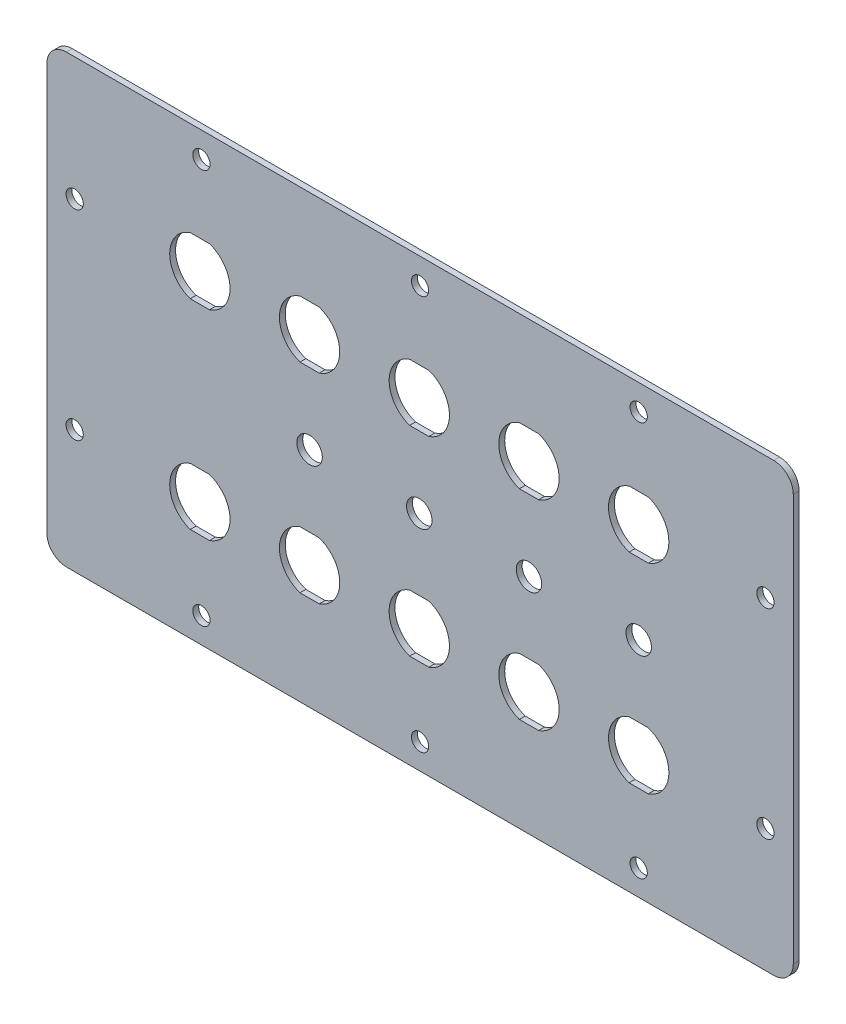
SolidWorks part; units mm, degrees
ref_plane "Front Plane" through (0, 0, 0) normal (0, 0, 1) x (1, 0, 0)
ref_plane "Top Plane" through (0, 0, 0) normal (0, 1, 0) x (1, 0, 0)
ref_plane "Right Plane" through (0, 0, 0) normal (1, 0, 0) x (0, 0, -1)
sketch "Sketch1" plane through (0, 0, 0) normal (0, 0, 1) x (1, 0, 0)
  line L1 (0, 0) -> (190.5, 0)
  line L2 (0, 0) -> (0, 113.82)
  line L3 (0, 113.82) -> (190.5, 113.82)
  line L4 (190.5, 0) -> (190.5, 113.82)
  dimension "D1" = 190.5
  dimension "D2" = 113.82
extrude "Boss-Extrude1" add sketch "Sketch1" along normal blind 1.5
sketch "Sketch2" plane through (0, 0, 0) normal (0, 0, -1) x (-1, 0, 0)
  line L0 (-190.5, 56.91) -> (-183.4, 56.91) construction
  line L1 (-190.5, 0) -> (-190.5, 113.82) construction
  line L2 (-183.4, 56.91) -> (-183.4, 82.41) construction
  line L3 (-183.4, 56.91) -> (-183.4, 31.41) construction
  line L5 (-95.25, 0) -> (-95.25, 113.82) construction
  line L6 (0, 0) -> (-190.5, 0) construction
  line L7 (-190.5, 113.82) -> (0, 113.82) construction
  circle A0 centre (-183.4, 82.41) radius 2.2
  circle A1 centre (-183.4, 31.41) radius 2.2
  circle A2 centre (-7.1, 31.41) radius 2.2
  circle A3 centre (-7.1, 82.41) radius 2.2
  dimension "D3" = 4.4
  dimension "D4" = 4.4
  dimension "D1" = 25.5
  dimension "D2" = 25.5
  dimension "D5" = 7.1
extrude "Cut-Extrude1" cut sketch "Sketch2" against normal through all
sketch "Sketch3" plane through (0, 0, 0) normal (0, 0, -1) x (-1, 0, 0)
  line L0 (-45.2086, 107.31) -> (-45.2086, 6.51) construction
  line L1 (-45.2086, 56.91) -> (0, 56.91) construction
  line L2 (0, 113.82) -> (0, 0) construction
  line L3 (-95.25, 0) -> (-95.25, 48.2071) construction
  line L4 (0, 0) -> (-190.5, 0) construction
  circle A0 centre (-95.25, 107.31) radius 2.2
  circle A1 centre (-39.45, 107.31) radius 2.2
  circle A2 centre (-151.05, 107.31) radius 2.2
  circle A3 centre (-39.45, 6.51) radius 2.2
  circle A4 centre (-95.25, 6.51) radius 2.2
  circle A5 centre (-151.05, 6.51) radius 2.2
  point P22 (0, 0)
  point P23 (0, 0)
  dimension "D2" = 4.4
  dimension "D3" = 4.4
  dimension "D4" = 55.8
  dimension "D1" = 100.8
extrude "Cut-Extrude2" cut sketch "Sketch3" against normal through all
sketch "Sketch4" plane through (0, 0, 0) normal (0, 0, -1) x (-1, 0, 0)
  line L0 (-153.4995, 89.71) -> (-148.6005, 89.71)
  line L1 (-153.4995, 75.11) -> (-148.6005, 75.11)
  line L2 (-151.05, 89.71) -> (-151.05, 90.11) construction
  line L3 (-190.5, 113.82) -> (0, 113.82) construction
  line L4 (-151.05, 75.11) -> (-151.05, 74.71) construction
  line L5 (-190.5, 56.91) -> (-180.4107, 56.91) construction
  line L6 (-190.5, 0) -> (-190.5, 113.82) construction
  line L7 (-153.4995, 24.11) -> (-148.6005, 24.11)
  line L8 (-153.4995, 38.71) -> (-148.6005, 38.71)
  line L9 (-125.4995, 75.11) -> (-120.6005, 75.11)
  line L10 (-125.4995, 89.71) -> (-120.6005, 89.71)
  line L11 (-125.4995, 38.71) -> (-120.6005, 38.71)
  line L12 (-125.4995, 24.11) -> (-120.6005, 24.11)
  line L13 (-97.4995, 75.11) -> (-92.6005, 75.11)
  line L14 (-97.4995, 89.71) -> (-92.6005, 89.71)
  line L15 (-97.4995, 38.71) -> (-92.6005, 38.71)
  line L16 (-97.4995, 24.11) -> (-92.6005, 24.11)
  line L17 (-69.4995, 75.11) -> (-64.6005, 75.11)
  line L18 (-69.4995, 89.71) -> (-64.6005, 89.71)
  line L19 (-69.4995, 38.71) -> (-64.6005, 38.71)
  line L20 (-69.4995, 24.11) -> (-64.6005, 24.11)
  line L21 (-41.4995, 75.11) -> (-36.6005, 75.11)
  line L22 (-41.4995, 89.71) -> (-36.6005, 89.71)
  line L23 (-41.4995, 38.71) -> (-36.6005, 38.71)
  line L24 (-41.4995, 24.11) -> (-36.6005, 24.11)
  arc A0 (-148.6005, 75.11) -> (-148.6005, 89.71) centre (-151.05, 82.41) ccw
  circle A2 centre (-151.05, 56.91) radius 3.25
  arc A3 (-153.4995, 89.71) -> (-153.4995, 75.11) centre (-151.05, 82.41) ccw
  arc A4 (-153.4995, 24.11) -> (-153.4995, 38.71) centre (-151.05, 31.41) cw
  arc A5 (-148.6005, 38.71) -> (-148.6005, 24.11) centre (-151.05, 31.41) cw
  arc A6 (-120.6005, 75.11) -> (-120.6005, 89.71) centre (-123.05, 82.41) ccw
  arc A7 (-125.4995, 89.71) -> (-125.4995, 75.11) centre (-123.05, 82.41) ccw
  circle A8 centre (-123.05, 56.91) radius 3.25
  arc A9 (-125.4995, 24.11) -> (-125.4995, 38.71) centre (-123.05, 31.41) cw
  arc A10 (-120.6005, 38.71) -> (-120.6005, 24.11) centre (-123.05, 31.41) cw
  arc A11 (-92.6005, 75.11) -> (-92.6005, 89.71) centre (-95.05, 82.41) ccw
  arc A12 (-97.4995, 89.71) -> (-97.4995, 75.11) centre (-95.05, 82.41) ccw
  circle A13 centre (-95.05, 56.91) radius 3.25
  arc A14 (-97.4995, 24.11) -> (-97.4995, 38.71) centre (-95.05, 31.41) cw
  arc A15 (-92.6005, 38.71) -> (-92.6005, 24.11) centre (-95.05, 31.41) cw
  arc A16 (-64.6005, 75.11) -> (-64.6005, 89.71) centre (-67.05, 82.41) ccw
  arc A17 (-69.4995, 89.71) -> (-69.4995, 75.11) centre (-67.05, 82.41) ccw
  circle A18 centre (-67.05, 56.91) radius 3.25
  arc A19 (-69.4995, 24.11) -> (-69.4995, 38.71) centre (-67.05, 31.41) cw
  arc A20 (-64.6005, 38.71) -> (-64.6005, 24.11) centre (-67.05, 31.41) cw
  arc A21 (-36.6005, 75.11) -> (-36.6005, 89.71) centre (-39.05, 82.41) ccw
  arc A22 (-41.4995, 89.71) -> (-41.4995, 75.11) centre (-39.05, 82.41) ccw
  arc A24 (-41.4995, 24.11) -> (-41.4995, 38.71) centre (-39.05, 31.41) cw
  arc A25 (-36.6005, 38.71) -> (-36.6005, 24.11) centre (-39.05, 31.41) cw
  circle A26 centre (-39.05, 56.91) radius 3.25 [skipped]
  dimension "D1" = 15.4
  dimension "D2" = 5
  dimension "D3" = 6.5
  dimension "D6" = 31.41
  dimension "D4" = 0.4
  dimension "D5" = 0.4
extrude "Cut-Extrude3" cut sketch "Sketch4" against normal through all
fillet "Fillet1" radius 5 2 edges at (190.5, 0, 0.75) (190.5, 113.82, 0.75)
fillet "Fillet2" radius 5 2 edges at (0, 0, 0.75) (0, 113.82, 0.75)
